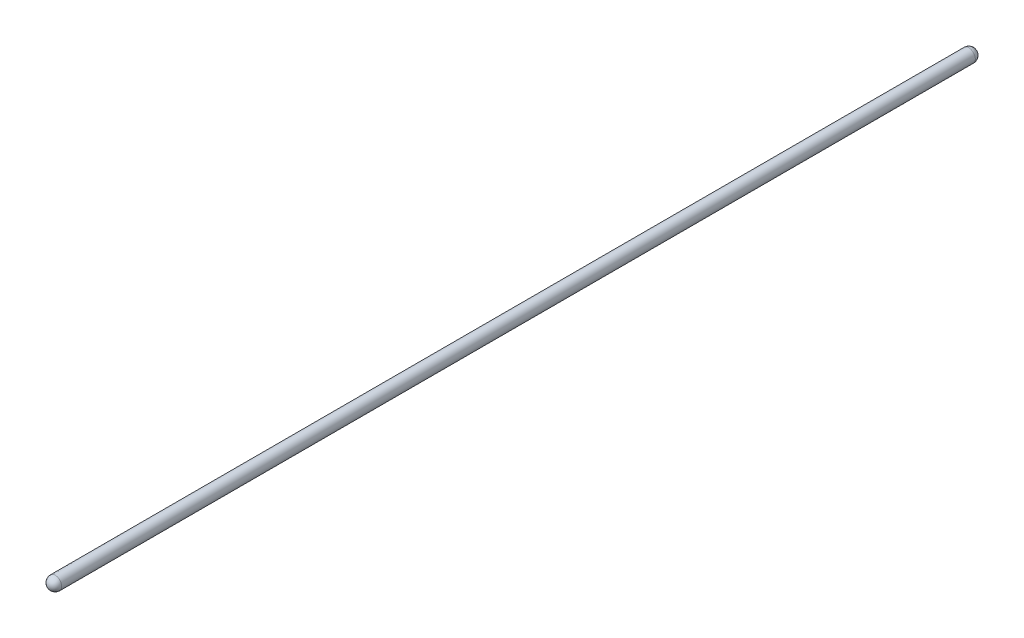
SolidWorks part; units mm, degrees
ref_plane "Front Plane" through (0, 0, 0) normal (0, 0, 1) x (1, 0, 0)
ref_plane "Top Plane" through (0, 0, 0) normal (0, 1, 0) x (1, 0, 0)
ref_plane "Right Plane" through (0, 0, 0) normal (1, 0, 0) x (0, 0, -1)
sketch "Sketch1" plane through (0, 0, 0) normal (0, 1, 0) x (1, 0, 0)
  line L0 (0, 0) -> (0, 9.525) construction
  line L1 (0, 0) -> (9.525, 0) construction
  line L2 (0, 0) -> (0, -1331.0387) construction
  line L3 (0, -1331.0387) -> (9.525, -1331.0387) construction
  line L4 (0, -1331.0387) -> (0, -1340.5637) construction
  line L5 (9.525, 0) -> (9.525, -1331.0387)
  line L6 (0, 9.525) -> (0, -1340.5637)
  arc A1 (0, 9.525) -> (9.525, 0) centre (0, 0) cw
  arc A2 (9.525, -1331.0387) -> (0, -1340.5637) centre (0, -1331.0387) cw
revolve "Revolve1" add sketch "Sketch1" angle 360 about L6
